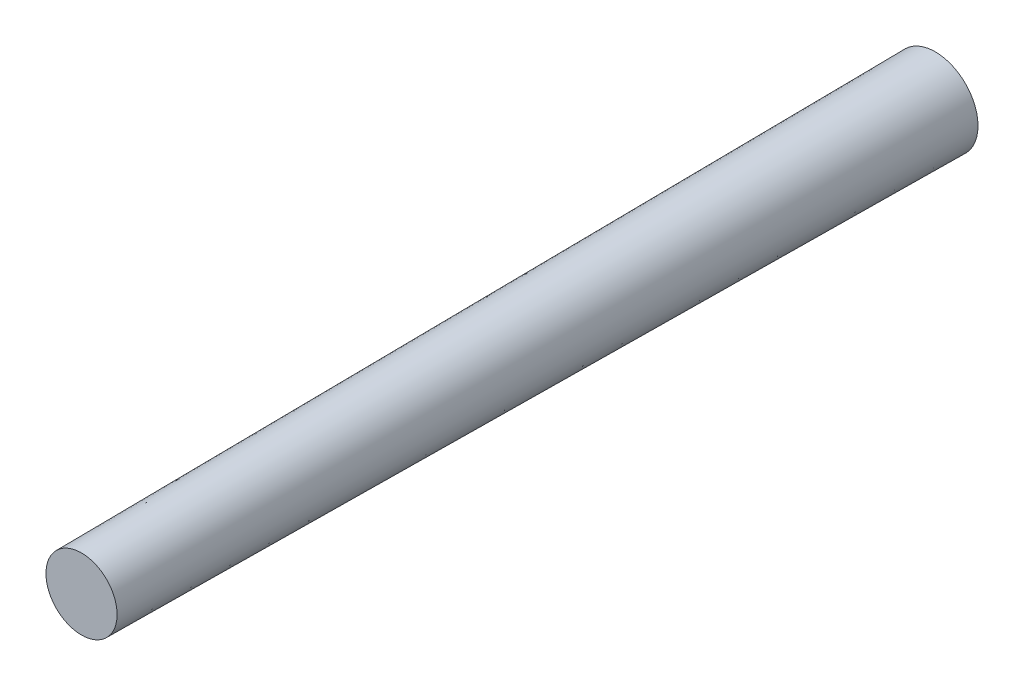
SolidWorks part; units mm, degrees
ref_plane "Front Plane" through (0, 0, 0) normal (0, 0, 1) x (1, 0, 0)
ref_plane "Top Plane" through (0, 0, 0) normal (0, 1, 0) x (1, 0, 0)
ref_plane "Right Plane" through (0, 0, 0) normal (1, 0, 0) x (0, 0, -1)
sketch "Sketch1" plane through (0, 0, 0) normal (0, 0, 1) x (1, 0, 0)
  circle A0 centre (0, 0) radius 3
  dimension "D1" = 6
extrude "Boss-Extrude1" add sketch "Sketch1" along normal blind 60 draft 0.477
